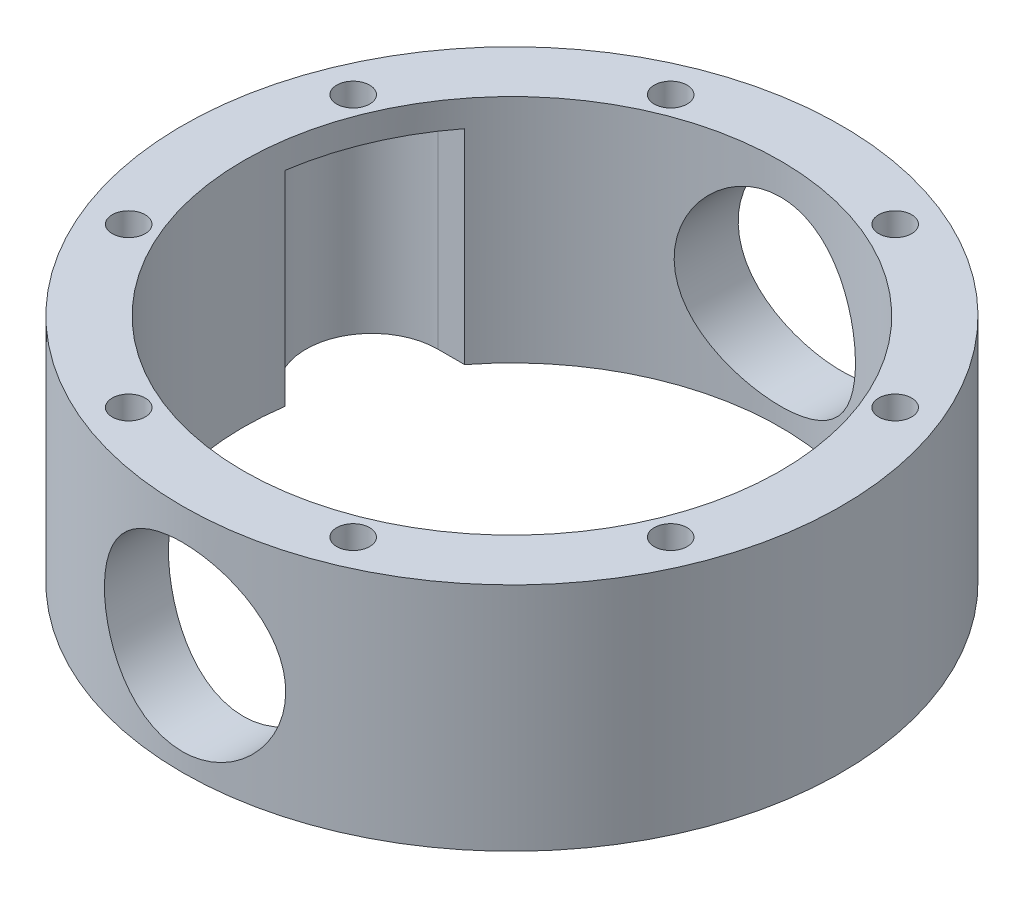
SolidWorks part; units mm, degrees
material "1.0037 (S235JR)"
ref_plane "Front Plane" through (0, 0, 0) normal (0, 0, 1) x (1, 0, 0)
ref_plane "Top Plane" through (0, 0, 0) normal (0, 1, 0) x (1, 0, 0)
ref_plane "Right Plane" through (0, 0, 0) normal (1, 0, 0) x (0, 0, -1)
sketch "Sketch1" plane through (0, 0, 0) normal (0, 1, 0) x (1, 0, 0)
  circle A0 centre (0, 0) radius 100
  circle A1 centre (0, 0) radius 81.5
  dimension "D1" = 200
  dimension "D2" = 163
extrude "Boss-Extrude1" add sketch "Sketch1" along normal mid plane 70
sketch "Sketch3" plane through (0, 0, 0) normal (0, 0, 1) x (1, 0, 0)
  line L0 (-100, -35) -> (100, -35) construction
  circle A0 centre (0, -2) radius 27.5
  dimension "D1" = 55
  dimension "D2" = 33
extrude "Cut-Extrude1" cut sketch "Sketch3" against normal through all both and the other way through all
sketch "Sketch4" plane through (0, 35, 0) normal (0, 1, 0) x (1, 0, 0)
  line L0 (-34.0588, 82.2253) -> (0, 0) construction
  line L1 (0, 0) -> (0, 83.0322) construction
  circle A0 centre (-34.0588, 82.2253) radius 5
  dimension "D1" = 10
  dimension "D2" = 89
  dimension "D3" = 22.5
extrude "Cut-Extrude2" cut sketch "Sketch4" against normal up to next (70 mm away)
pattern_circular "CirPattern1" count 8 over 360 about axis through (0, 0, 0) along (0, 1, 0) of "Cut-Extrude2"
sketch "Sketch5" plane through (0, -35, 0) normal (0, -1, 0) x (1, 0, 0)
  line L0 (0, 0) -> (0, -10) construction
  line L1 (-72.5, -10) -> (-72.5, -50) construction
  line L2 (-72.5, -10) -> (72.5, -10)
  line L3 (72.5, -10) -> (72.5, -50) construction
  line L4 (-72.5, -50) -> (72.5, -50)
  arc A0 (-72.5, -10) -> (-72.5, -50) centre (-72.5, -30) ccw
  arc A1 (72.5, -10) -> (72.5, -50) centre (72.5, -30) cw
  dimension "D1" = 10
  dimension "D2" = 145
  dimension "D3" = 40
extrude "Cut-Extrude3" cut sketch "Sketch5" against normal blind 62
